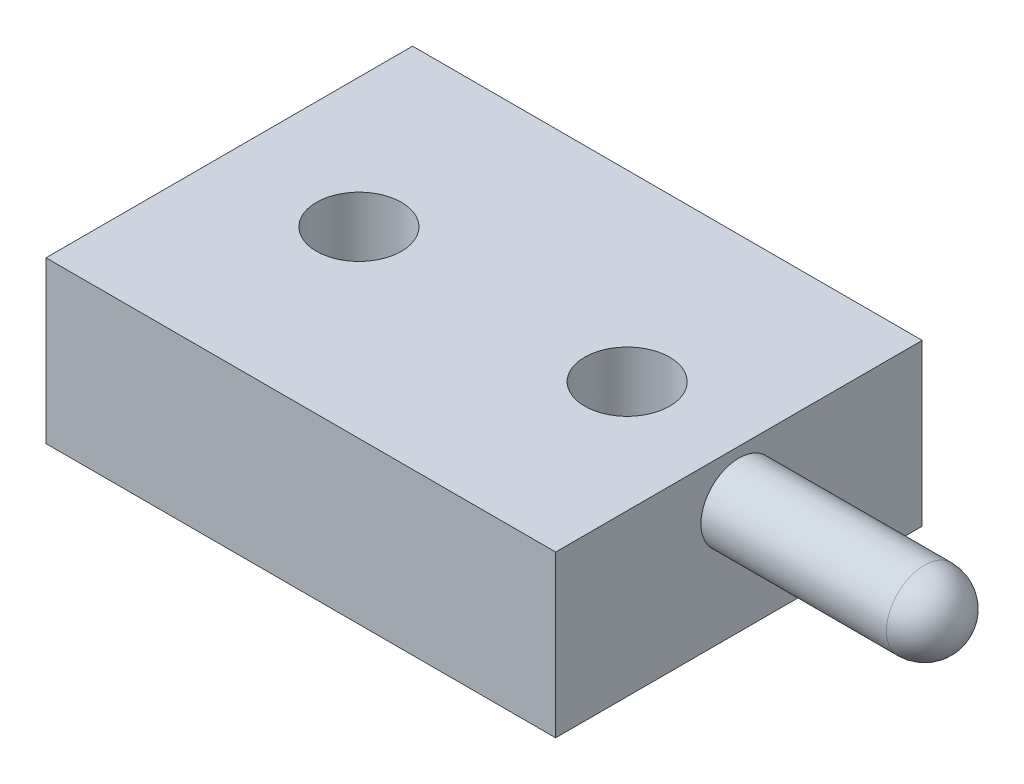
SolidWorks part; units mm, degrees
material "PBT (一般用)"
ref_plane "Front Plane" through (0, 0, 0) normal (0, 0, 1) x (1, 0, 0)
ref_plane "Top Plane" through (0, 0, 0) normal (0, 1, 0) x (1, 0, 0)
ref_plane "Right Plane" through (0, 0, 0) normal (1, 0, 0) x (0, 0, -1)
sketch "Sketch1" plane through (0, 0, 0) normal (0, 1, 0) x (1, 0, 0)
  line L1 (0, 0) -> (5.7, 0)
  line L2 (0, 0) -> (0, -4.1)
  line L3 (0, -4.1) -> (5.7, -4.1)
  line L4 (5.7, 0) -> (5.7, -4.1)
  dimension "D1" = 5.7
  dimension "D2" = 4.1
extrude "Boss-Extrude1" add sketch "Sketch1" against normal blind 1.8
sketch "Sketch3" plane through (5.7, 0, 0) normal (1, 0, 0) x (0, 0, -1)
  line L0 (-4.9495, -0.54) -> (1.0417, -0.54)
  line L1 (-4.1, -1.8) -> (0, -1.8) construction
  circle A0 centre (-2.05, -0.54) radius 0.425
  dimension "D1" = 1.26
extrude "Boss-Extrude3" add sketch "Sketch3" along normal blind 2.5 contours A0
fillet "Fillet2" radius 0.425 1 edges at (8.2, -0.54, 1.625)
hole_wizard "M1.2x0.25 Tapped Hole1" positions "Sketch5" profile "Sketch4" tap size "M1.2x0.25" standard "ANSI Metric"
sketch "Sketch5" plane through (0, -1.8, 0) normal (0, -1, 0) x (-1, 0, 0)
  line L0 (-5.7, -4.1) -> (-5.7, 0) construction
  point P0 (-4.45, -2.05)
  point P2 (-1.45, -2.05)
  dimension "D1" = 1.25
  dimension "D2" = 3
sketch "Sketch4" plane through (4.45, -1.8, 2.05) normal (1, 0, 0) x (0, 0, -1)
  line L0 (0, 0) -> (0, 3.4354)
  line L1 (0, 3.4354) -> (0.475, 3.15)
  line L2 (0.475, 3.15) -> (0.475, 0)
  line L5 (0.475, 0) -> (0, 0)
  line L10 (0, 3.4354) -> (-0.475, 3.15) construction
  line L11 (0, -6.35) -> (0, 107.95) construction
  dimension "Tap Drill Dia." = 0.95
  dimension "Tap Drill Depth" = 3.15
  dimension "Drill Angle" = 118
cosmetic thread "Hole Thread1" parameters "D1"=2, "D2"=1.2
cosmetic thread "Hole Thread2" parameters "D1"=2, "D2"=1.2
